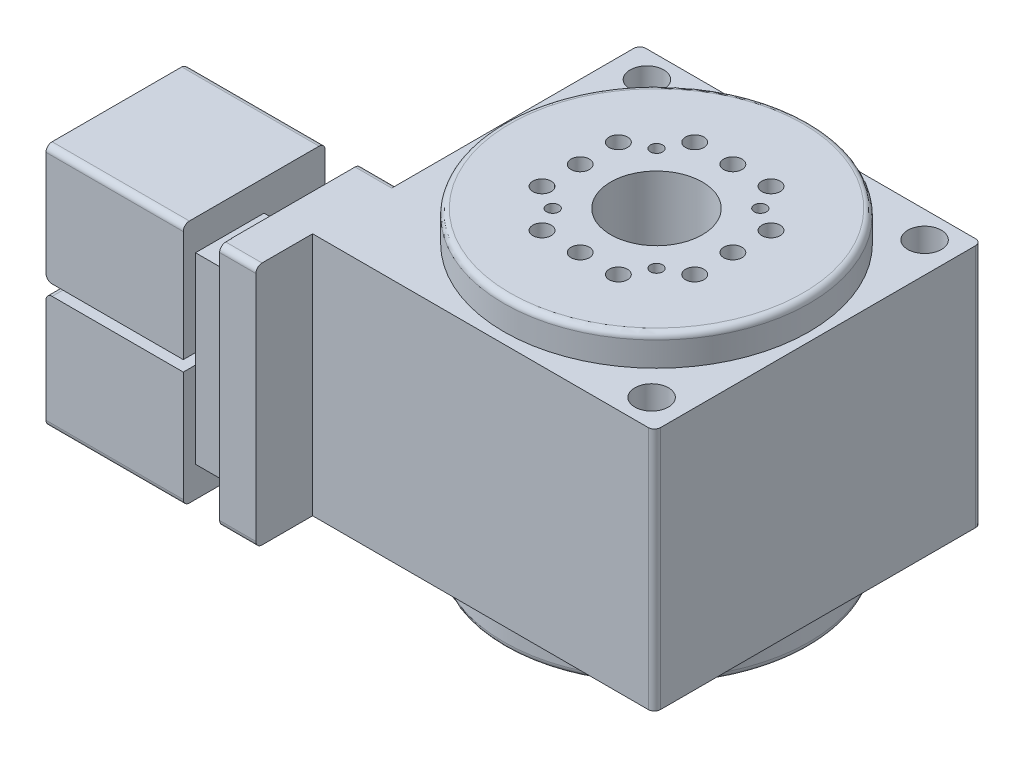
SolidWorks part; units mm, degrees
ref_plane "前视基准面" through (0, 0, 0) normal (0, 0, 1) x (1, 0, 0)
ref_plane "上视基准面" through (0, 0, 0) normal (0, 1, 0) x (1, 0, 0)
ref_plane "右视基准面" through (0, 0, 0) normal (1, 0, 0) x (0, 0, -1)
sketch "草图1" plane through (0, 0, 0) normal (0, 1, 0) x (1, 0, 0)
  line L0 (-59.1198, 53.6429) -> (52.8269, 53.6429)
  line L1 (52.8269, 53.6429) -> (52.8269, -53.5231)
  line L2 (52.8269, -53.5231) -> (-59.1198, -53.5231)
  line L3 (-59.1198, -53.5231) -> (-59.1198, -72.0798)
  line L4 (-59.1198, -72.0798) -> (-127.8826, -72.0798)
  line L5 (-127.8826, -72.0798) -> (-127.8826, -25.632)
  line L6 (-127.8826, -25.632) -> (-59.1198, -25.632)
  line L7 (-59.1198, -25.632) -> (-59.1198, 53.6429)
  circle A0 centre (0, 0) radius 50
  dimension "D1" = 100
extrude "凸台-拉伸1" add sketch "草图1" along normal blind 80
fillet "圆角1" radius 2 8 edges at (-127.8826, 40, 25.632) (-93.5012, 80, 72.0798) (-93.5012, 0, 72.0798) (-93.5012, 0, 25.632) (-93.5012, 80, 25.632) (-59.1198, 40, -53.6429) (52.8269, 40, -53.6429) (52.8269, 40, 53.5231)
sketch "草图2" plane through (0, 80, 0) normal (0, 1, 0) x (1, 0, 0)
  circle A0 centre (-48.1196, 44.9793) radius 5.5
  circle A1 centre (42.8264, 44.9793) radius 5.5
  circle A2 centre (42.8264, -44.4209) radius 5.5
  dimension "D1" = 11
  dimension "D2" = 11
  dimension "D3" = 11
extrude "切除-拉伸1" cut sketch "草图2" against normal blind 80
sketch "草图3" plane through (0, 0, 72.0798) normal (0, 0, 1) x (1, 0, 0)
  line L0 (-82.9193, 84.2367) -> (-82.9193, -7.9416)
  line L1 (-82.9193, 84.2367) -> (-71.0132, 84.2367)
  line L2 (-82.9193, -7.9416) -> (-71.0132, -7.9416)
  line L3 (-71.0132, 84.2367) -> (-71.0132, -7.9416)
extrude "切除-拉伸2" cut sketch "草图3" against normal blind 4
sketch "草图4" plane through (0, 80, 0) normal (0, 1, 0) x (1, 0, 0)
  line L0 (-82.9193, -68.0798) -> (-82.9193, -25.632)
  line L1 (-82.9193, -68.0798) -> (-71.1091, -68.0798)
  line L2 (-82.9193, -25.632) -> (-71.1091, -25.632)
  line L3 (-71.1091, -68.0798) -> (-71.1091, -25.632)
  line L4 (-125.8826, -25.632) -> (-59.1198, -25.632) construction
extrude "切除-拉伸3" cut sketch "草图4" against normal blind 10
sketch "草图5" plane through (0, 0, 0) normal (0, -1, 0) x (1, 0, 0)
  line L0 (-82.9193, 68.0798) -> (-82.9193, 22.592)
  line L1 (-82.9193, 68.0798) -> (-70.9773, 68.0798)
  line L2 (-82.9193, 22.592) -> (-70.9773, 22.592)
  line L3 (-70.9773, 68.0798) -> (-70.9773, 22.592)
extrude "切除-拉伸4" cut sketch "草图5" against normal blind 10
sketch "草图6" plane through (0, 0, 25.632) normal (0, 0, -1) x (-1, 0, 0)
  line L0 (71.1091, 70) -> (82.9193, 70)
  line L1 (71.1091, 70) -> (71.1091, 9.9217)
  line L2 (82.9193, 70) -> (82.9193, 9.9217)
  line L3 (71.1091, 9.9217) -> (82.9193, 9.9217)
extrude "切除-拉伸5" cut sketch "草图6" against normal blind 20
sketch "草图7" plane through (0, 0, 25.632) normal (0, 0, -1) x (-1, 0, 0)
  line L0 (125.8826, 41.671) -> (82.9193, 41.671)
  line L1 (125.8826, 2) -> (125.8826, 78) construction
  line L2 (82.9193, 10) -> (82.9193, 70) construction
  line L3 (82.9193, 41.671) -> (82.9193, 38.1494)
  line L4 (82.9193, 2) -> (82.9193, 78) construction
  line L5 (82.9193, 38.1494) -> (125.8826, 38.1494)
  line L6 (125.8826, 38.1494) -> (132.649, 38.1494)
  line L7 (132.649, 38.1494) -> (132.649, 41.671)
  line L8 (132.649, 41.671) -> (125.8826, 41.671)
extrude "切除-拉伸7" cut sketch "草图7" against normal blind 50
fillet "圆角2" radius 2 6 edges at (-127.8826, 41.671, 49.8559) (-127.2968, 41.671, 26.2178) (-127.8826, 38.1494, 49.8559) (-127.2968, 38.1494, 26.2178) (-104.4009, 41.671, 25.632) (-104.4009, 38.1494, 25.632)
sketch "草图8" plane through (0, 0, 0) normal (0, 1, 0) x (1, 0, 0)
  circle A0 centre (0, 0) radius 50
extrude "凸台-拉伸2" add sketch "草图8" along normal blind 90
sketch "草图9" plane through (0, 90, 0) normal (0, 1, 0) x (1, 0, 0)
  circle A0 centre (0, 0) radius 50
extrude "凸台-拉伸3" add sketch "草图9" against normal blind 100
fillet "圆角3" radius 2 2 edges at (0, 90, 50) (0, -10, 50)
sketch "草图10" plane through (0, -10, 0) normal (0, -1, 0) x (1, 0, 0)
  circle A0 centre (0, 0) radius 15
  dimension "D1" = 30
extrude "切除-拉伸8" cut sketch "草图10" against normal blind 100
sketch "草图11" plane through (0, -10, 0) normal (0, -1, 0) x (1, 0, 0)
  circle A0 centre (25, 0) radius 3
  circle A1 centre (25, 12.5) radius 3
  circle A2 centre (25, -12.5) radius 3
  dimension "D2" = 6
  dimension "D4" = 6
  dimension "D5" = 6
  dimension "D1" = 12.5
  dimension "D3" = 25
extrude "切除-拉伸9" cut sketch "草图11" against normal blind 10
pattern_circular "阵列(圆周)1" count 4 over 360 about axis through (0, 0, 0) along (0, 1, 0) of "切除-拉伸9"
sketch "草图12" plane through (0, 90, 0) normal (0, 1, 0) x (1, 0, 0)
  circle A0 centre (-12.5, 25) radius 3 construction
  circle A1 centre (0, 25) radius 3 construction
  circle A2 centre (12.5, 25) radius 3 construction
  circle A3 centre (-12.5, 25) radius 3
  circle A4 centre (0, 25) radius 3
  circle A5 centre (12.5, 25) radius 3
extrude "切除-拉伸10" cut sketch "草图12" against normal blind 10
pattern_circular "阵列(圆周)2" count 4 over 360 about axis through (0, 0, 0) along (0, 1, 0) of "切除-拉伸10"
sketch "草图13" plane through (0, -10, 0) normal (0, -1, 0) x (1, 0, 0)
  circle A0 centre (17, 17) radius 2
  dimension "D3" = 4
extrude "切除-拉伸11" cut sketch "草图13" against normal blind 10
pattern_circular "阵列(圆周)3" count 4 over 360 about axis through (0, 0, 0) along (0, 1, 0) of "切除-拉伸11"
sketch "草图14" plane through (0, 90, 0) normal (0, 1, 0) x (1, 0, 0)
  circle A0 centre (-17, -17) radius 2 construction
  circle A1 centre (-17, 17) radius 2 construction
  circle A2 centre (17, 17) radius 2 construction
  circle A3 centre (17, -17) radius 2 construction
  circle A4 centre (-17, -17) radius 2
  circle A5 centre (-17, 17) radius 2
  circle A6 centre (17, 17) radius 2
  circle A7 centre (17, -17) radius 2
extrude "切除-拉伸12" cut sketch "草图14" against normal blind 10
